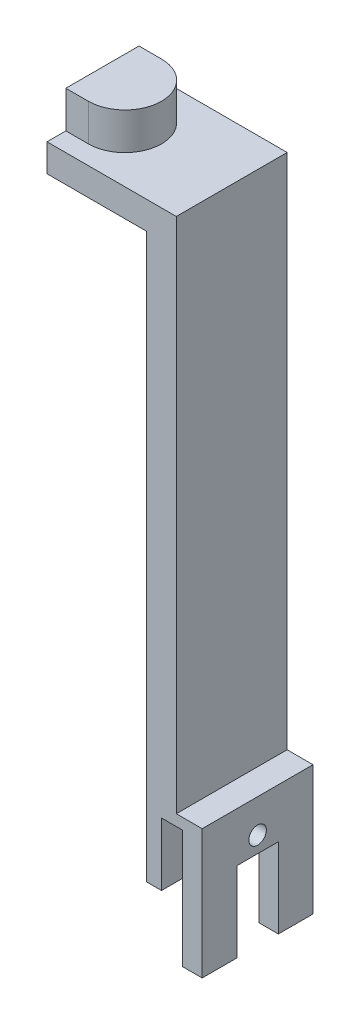
SolidWorks part; units mm, degrees
ref_plane "정면" through (0, 0, 0) normal (0, 0, 1) x (1, 0, 0)
ref_plane "윗면" through (0, 0, 0) normal (0, 1, 0) x (1, 0, 0)
ref_plane "우측면" through (0, 0, 0) normal (1, 0, 0) x (0, 0, -1)
sketch "스케치1" plane through (0, 0, 0) normal (0, 1, 0) x (1, 0, 0)
  line L0 (-104.0602, 0) -> (112.3308, 0) construction
  line L1 (0, 61.7293) -> (0, -68.6466) construction
  line L3 (7.5, -15) -> (-7.5, -15)
  line L4 (7.5, -15) -> (7.5, 15)
  line L5 (7.5, 15) -> (-7.5, 15)
  line L6 (-7.5, -15) -> (-7.5, 15)
  line L7 (7.5, -15) -> (-7.5, 15) construction
  line L8 (7.5, 15) -> (-7.5, -15) construction
  point P5 (0, 0)
  dimension "D1" = 30
  dimension "D2" = 15
extrude "보스-돌출1" add sketch "스케치1" along normal blind 20
sketch "스케치2" plane through (0, 0, 15) normal (0, 0, 1) x (1, 0, 0)
  line L1 (-3.5, 0) -> (2.2, 0)
  line L2 (-3.5, 0) -> (-3.5, 17)
  line L3 (-3.5, 17) -> (2.2, 17)
  line L4 (2.2, 0) -> (2.2, 17)
  line L5 (-7.5, 20) -> (-7.5, 0) construction
  line L7 (-7.5, 20) -> (7.5, 20) construction
  line L8 (-7.5, 0) -> (7.5, 0) construction
  point P4 (0, 0)
  point P5 (0, 0)
  point P12 (0, 0)
  point P13 (0, 0)
  dimension "D1" = 4
  dimension "D2" = 5.7
  dimension "D3" = 3
extrude "컷-돌출1" cut sketch "스케치2" against normal through all
sketch "스케치3" plane through (0, 20, 0) normal (0, 1, 0) x (1, 0, 0)
  line L0 (-7.5, -15) -> (7.5, -15) construction
  line L1 (-7.5, 15) -> (0.5, 15)
  line L2 (-7.5, 15) -> (-7.5, -15)
  line L3 (-7.5, -15) -> (0.5, -15)
  line L4 (0.5, 15) -> (0.5, -15)
  dimension "D1" = 8
extrude "보스-돌출2" add sketch "스케치3" along normal blind 150
sketch "스케치4" plane through (7.5, 0, 0) normal (1, 0, 0) x (0, 0, -1)
  line L0 (-15, 0) -> (15, 0) construction
  circle A0 centre (0, 11) radius 2.375
  dimension "D1" = 4.75
  dimension "D2" = 11
extrude "컷-돌출2" cut sketch "스케치4" against normal through all
sketch "스케치5" plane through (-7.5, 0, 0) normal (-1, 0, 0) x (0, 0, 1)
  line L0 (15, 170) -> (15, 0) construction
  line L1 (-15, 170) -> (15, 170)
  line L2 (-15, 170) -> (-15, 152.5)
  line L3 (-15, 152.5) -> (15, 152.5)
  line L4 (15, 170) -> (15, 152.5)
  dimension "D1" = 17.5
extrude "보스-돌출3" add sketch "스케치5" along normal blind 27
sketch "스케치6" plane through (0, 170, 0) normal (0, 1, 0) x (1, 0, 0)
  line L0 (-34.5, 9.9) -> (-34.5, -9.9)
  line L1 (-28.4, 9.9) -> (-34.5, 9.9)
  line L2 (0.5, 15) -> (-34.5, 15) construction
  line L3 (-34.5, -9.9) -> (-28.4, -9.9)
  line L4 (-34.5, -15) -> (0.5, -15) construction
  line L5 (-34.5, 15) -> (0.5, 15)
  line L6 (-34.5, 15) -> (-34.5, -15)
  line L7 (-34.5, -15) -> (0.5, -15)
  line L8 (0.5, 15) -> (0.5, -15)
  line L9 (0.5, -15) -> (0.5, 15) construction
  arc A1 (-28.4, -9.9) -> (-28.4, 9.9) centre (-28.4, 0) ccw
  line M4 (0.5, 15) -> (-34.5, 15)
  line M5 (-34.5, 15) -> (-34.5, -15)
  line M6 (-34.5, -15) -> (0.5, -15)
  line M7 (0.5, -15) -> (0.5, 15)
  dimension "D1" = 9.9
  dimension "D3" = 15
  dimension "D4" = 9.9
  dimension "D2" = 16
  dimension "D5" = 19.8
extrude "컷-돌출3" cut sketch "스케치6" against normal blind 10 contours A1 L3 L1 M5 M6 M7 M4
sketch "스케치7" plane through (7.5, 0, 0) normal (1, 0, 0) x (0, 0, -1)
  line L0 (15, 20) -> (15, 0) construction
  line L1 (-15, 0) -> (15, 0)
  line L2 (-15, 0) -> (-15, -15)
  line L3 (-15, -15) -> (15, -15)
  line L4 (15, 0) -> (15, -15)
  dimension "D1" = 15
extrude "보스-돌출4" add sketch "스케치7" against normal blind 5.3
sketch "스케치8" plane through (7.5, 0, 0) normal (1, 0, 0) x (0, 0, -1)
  line L0 (-15, -15) -> (15, -15) construction
  line L1 (-5.625, -15) -> (5.625, -15)
  line L2 (-5.625, -15) -> (-5.625, 6.625)
  line L3 (-5.625, 6.625) -> (5.625, 6.625)
  line L4 (5.625, -15) -> (5.625, 6.625)
  circle A1 centre (0, 11) radius 2.375 construction
  dimension "D3" = 2
  dimension "D1" = 8
  dimension "D2" = 8
extrude "컷-돌출4" cut sketch "스케치8" against normal up to next
